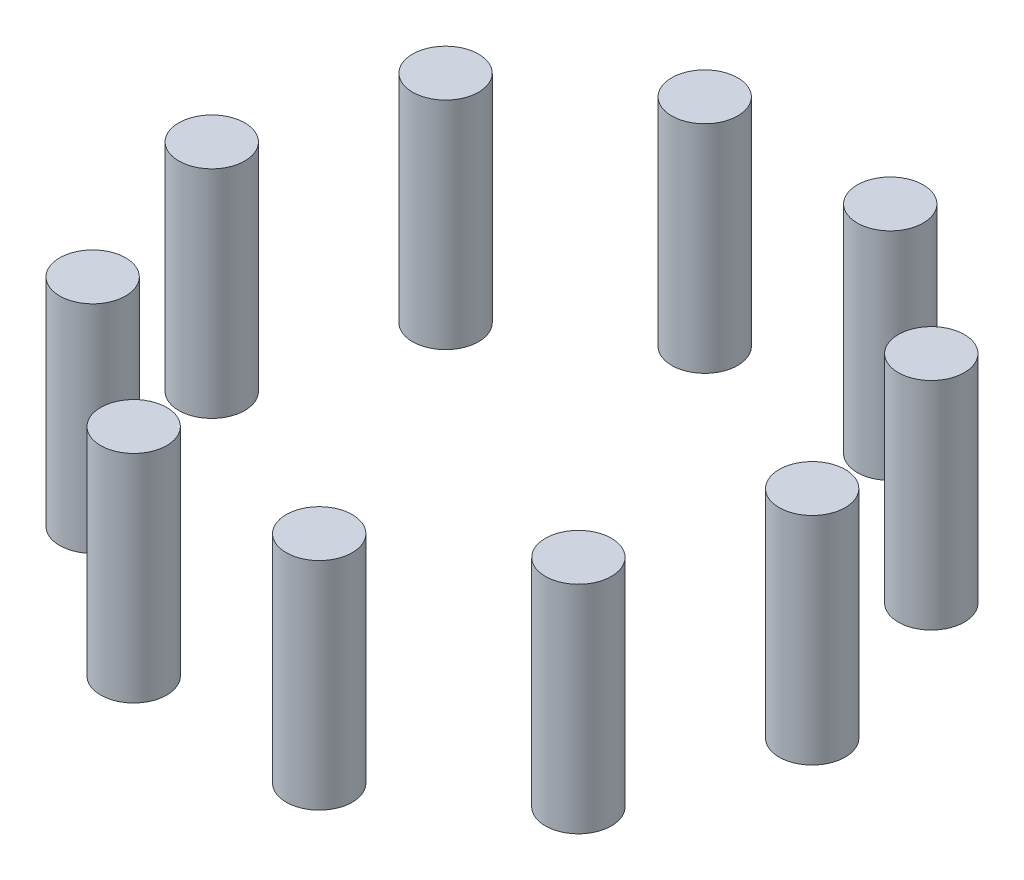
SolidWorks part; units mm, degrees
ref_plane "Front Plane" through (0, 0, 0) normal (0, 0, 1) x (1, 0, 0)
ref_plane "Top Plane" through (0, 0, 0) normal (0, 1, 0) x (1, 0, 0)
ref_plane "Right Plane" through (0, 0, 0) normal (1, 0, 0) x (0, 0, -1)
sketch "Sketch1" plane through (0, 0, 0) normal (0, 1, 0) x (1, 0, 0)
  circle A0 centre (0, 0) radius 50
  circle A1 centre (50, 0) radius 5.5
  circle A2 centre (40.4508, -29.3893) radius 5.5
  circle A3 centre (15.4508, -47.5528) radius 5.5
  circle A4 centre (-15.4508, -47.5528) radius 5.5
  circle A5 centre (-40.4508, -29.3893) radius 5.5
  circle A6 centre (-50, 0) radius 5.5
  circle A7 centre (-40.4508, 29.3893) radius 5.5
  circle A8 centre (-15.4508, 47.5528) radius 5.5
  circle A9 centre (15.4508, 47.5528) radius 5.5
  circle A10 centre (40.4508, 29.3893) radius 5.5
  point P25 (0, 0)
  dimension "D1" = 10
extrude "Boss-Extrude1" add sketch "Sketch1" along normal blind 36 contours A6 | A7 | A8 | A9 | A10 | A1 | A2 | A3 | A4 | A5
